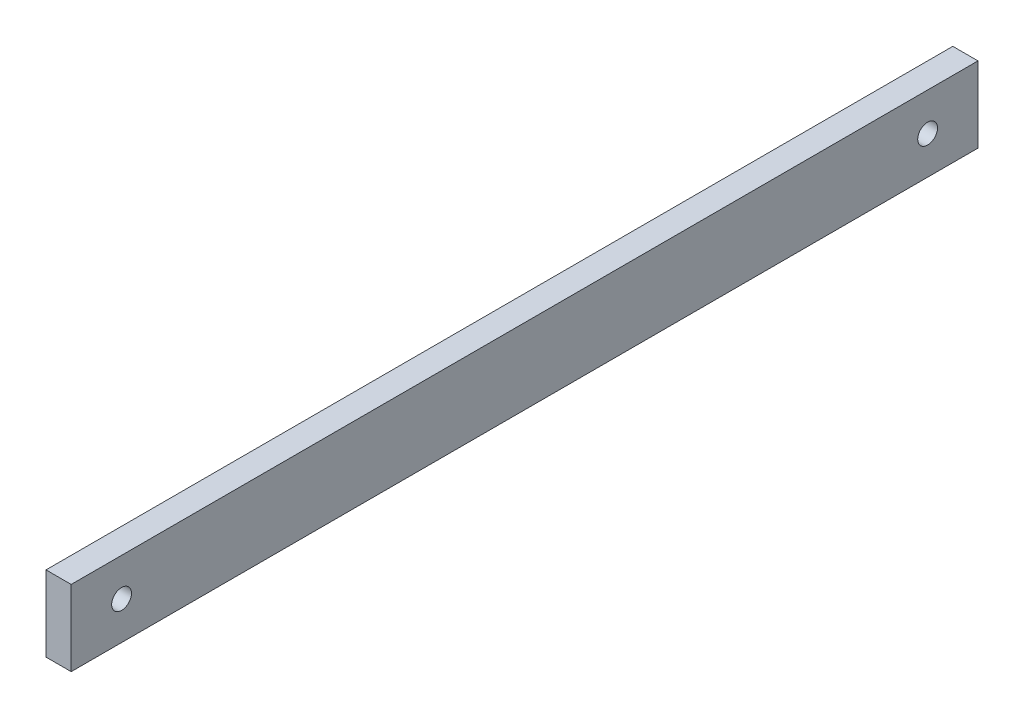
SolidWorks part; units mm, degrees
material "SS 304 (Default)"
ref_plane "Front Plane" through (0, 0, 0) normal (0, 0, 1) x (1, 0, 0)
ref_plane "Top Plane" through (0, 0, 0) normal (0, 1, 0) x (1, 0, 0)
ref_plane "Right Plane" through (0, 0, 0) normal (1, 0, 0) x (0, 0, -1)
sketch "Sketch1" plane through (0, 0, 0) normal (0, 0, 1) x (1, 0, 0)
  line L1 (-3.175, 9.525) -> (3.175, 9.525)
  line L2 (-3.175, 9.525) -> (-3.175, -9.525)
  line L3 (-3.175, -9.525) -> (3.175, -9.525)
  line L4 (3.175, 9.525) -> (3.175, -9.525)
  line L5 (-3.175, 9.525) -> (3.175, -9.525) construction
  line L6 (-3.175, -9.525) -> (3.175, 9.525) construction
  point P0 (0, 0)
  dimension "Width" = 6.35
  dimension "Height" = 19.05
extrude "Extrude1" add sketch "Sketch1" along normal mid plane 228.6
hole_wizard "M6x1.0 Tapped Hole1" positions "Sketch3" profile "Sketch2" tap size "M6x1.0" standard "Ansi Metric" end condition up to next
sketch "Sketch3" plane through (3.175, 0, 0) normal (1, 0, 0) x (0, 0, -1)
  line L0 (-101.6, 0) -> (101.6, 0) construction
  line L1 (114.3, -9.525) -> (114.3, 9.525) construction
  point P0 (-101.6, 0)
  point P1 (101.6, 0)
  dimension "D2" = 12.7
sketch "Sketch2" plane through (3.175, 0, 101.6) normal (0, 1, 0) x (0, 0, -1)
  line L0 (0, 0) -> (0, 6.35)
  line L1 (0, 6.35) -> (2.5, 6.35)
  line L2 (2.5, 6.35) -> (2.5, 0)
  line L5 (2.5, 0) -> (0, 0)
  line L11 (0, -6.35) -> (0, 107.95) construction
  dimension "Thru Tap Drill Dia." = 5
  dimension "Thru Tap Drill Depth" = 6.35
cosmetic thread "Hole Thread1" parameters "D2"=6
cosmetic thread "Hole Thread2" parameters "D2"=6
